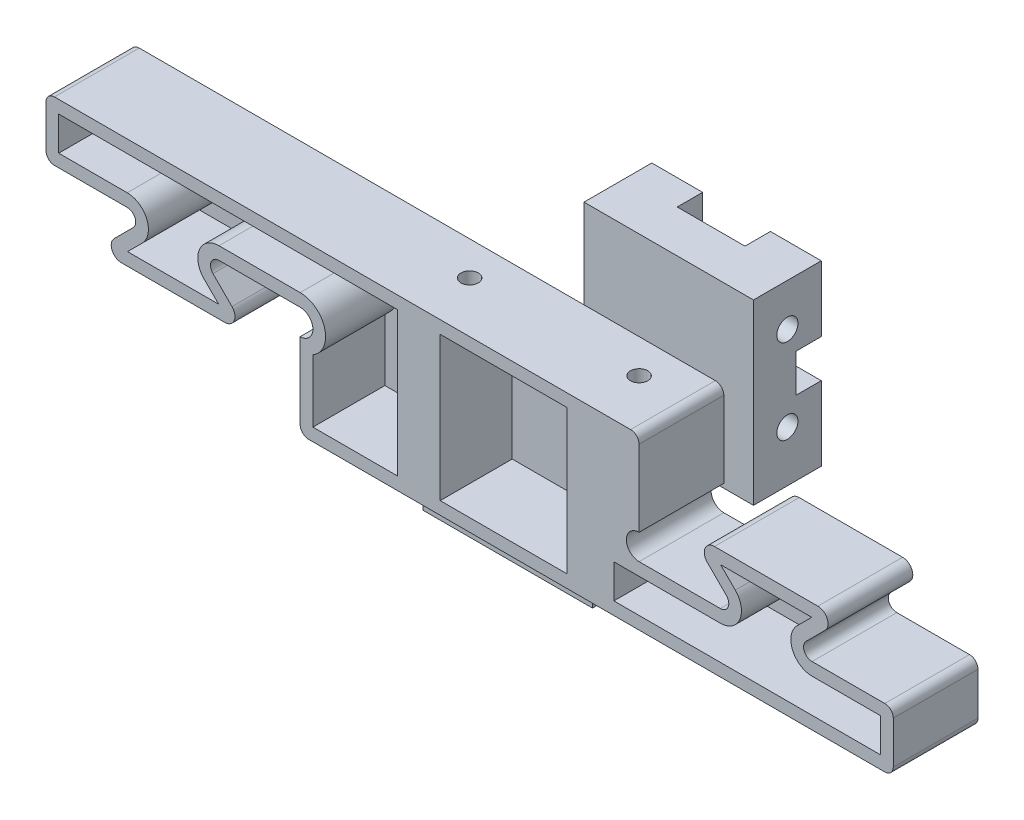
SolidWorks part; units mm, degrees
material "ABS"
ref_plane "Front Plane" through (0, 0, 0) normal (0, 0, 1) x (1, 0, 0)
ref_plane "Top Plane" through (0, 0, 0) normal (0, 1, 0) x (1, 0, 0)
ref_plane "Right Plane" through (0, 0, 0) normal (1, 0, 0) x (0, 0, -1)
sketch "Sketch1" plane through (0, 0, 0) normal (0, 0, 1) x (1, 0, 0)
  line L0 (-42.9118, -0.5) -> (16.2918, -0.5) construction
  line L2 (1, -1) -> (-19, -1)
  line L3 (1, -1) -> (1, -21)
  line L4 (1, -21) -> (-19, -21)
  line L5 (-19, -1) -> (-19, -21)
  line L6 (0, 0) -> (20, 0)
  line L7 (0, 0) -> (0, 20)
  line L8 (0, 20) -> (20, 20)
  line L9 (20, 0) -> (20, 20)
  dimension "D1" = 20
  dimension "D2" = 1
  dimension "D3" = 1
extrude "Boss-Extrude1" add sketch "Sketch1" along normal blind 8
hole_wizard "Tap Drill for M3 Tap1" positions "Sketch4" profile "Sketch3" hole size "M3" standard "DIN" end condition through all
sketch "Sketch4" plane through (20, 6.9301, -5.4582) normal (1, 0, 0) x (0, 0, -1)
  line L0 (-9.4582, 13.0699) -> (-9.4582, -24.1023) construction
  line L1 (-13.4582, 13.0699) -> (-5.4582, 13.0699) construction
  line L3 (-13.4582, 3.0699) -> (-15.7818, 3.0699) construction
  line L4 (-13.4582, -6.9301) -> (-13.4582, 13.0699) construction
  line L6 (-13.4582, -17.9301) -> (-14.075, -17.9301) construction
  line L7 (-13.4582, -27.9301) -> (-13.4582, -7.9301) construction
  point P0 (-9.4582, -12.9301)
  point P9 (-9.4582, 8.0699)
  point P11 (-9.4582, -1.9301)
  point P13 (-9.4582, -22.9301)
  dimension "D1" = 10
  dimension "D2" = 10
sketch "Sketch3" plane through (20, -6, 4) normal (0, 1, 0) x (0, 0, -1)
  line L0 (0, 0) -> (0, 39)
  line L1 (0, 39) -> (1.25, 39)
  line L2 (1.25, 39) -> (1.25, 0)
  line L5 (1.25, 0) -> (0, 0)
  line L11 (0, -6.35) -> (0, 107.95) construction
  dimension "Thru Hole Dia." = 2.5
  dimension "Thru Hole Depth" = 39
sketch "Sketch5" plane through (0, 0, 8) normal (0, 0, 1) x (1, 0, 0)
  line L0 (-19, -0.5) -> (20, -0.5) construction
  line L1 (1, -1) -> (-19, -1) construction
  line L2 (0, 0) -> (20, 0) construction
  line L3 (-19, -1) -> (-19, -21) construction
  line L4 (20, 0) -> (20, 20) construction
  line L6 (-13.5, -10.5) -> (14.5, -10.5)
  line L7 (-13.5, -10.5) -> (-13.5, 9.5)
  line L8 (-13.5, 9.5) -> (14.5, 9.5)
  line L9 (14.5, -10.5) -> (14.5, 9.5)
  line L10 (-13.5, -10.5) -> (14.5, 9.5) construction
  line L11 (-13.5, 9.5) -> (14.5, -10.5) construction
  point P10 (0.5, -0.5)
  dimension "D1" = 28
extrude "Boss-Extrude2" add sketch "Sketch5" along normal blind 8
hole_wizard "Tap Drill for M2.5 Tap1" positions "Sketch7" profile "Sketch6" hole size "M2.5" standard "DIN" end condition through all
sketch "Sketch7" plane through (0, -10.5, 0) normal (0, -1, 0) x (1, 0, 0)
  line L0 (-13.5, 12) -> (14.5, 12) construction
  line L1 (-13.5, 16) -> (-13.5, 8) construction
  line L2 (14.5, 16) -> (14.5, 8) construction
  line L4 (0.5, 16) -> (0.5, 18.815) construction
  line L5 (-13.5, 16) -> (14.5, 16) construction
  point P0 (-9.5, 12)
  point P1 (10.5, 12)
  dimension "D1" = 20
sketch "Sketch6" plane through (-9.5, -10.5, 12) normal (1, 0, 0) x (0, 0, -1)
  line L0 (0, 0) -> (0, 30.5)
  line L1 (0, 30.5) -> (1.025, 30.5)
  line L2 (1.025, 30.5) -> (1.025, 0)
  line L5 (1.025, 0) -> (0, 0)
  line L11 (0, -6.35) -> (0, 107.95) construction
  dimension "Thru Hole Dia." = 2.05
  dimension "Thru Hole Depth" = 30.5
sketch "Sketch16" plane through (0, 9.5, 0) normal (0, 1, 0) x (1, 0, 0)
  line L1 (-13.5, -16) -> (14.5, -16)
  line L2 (-13.5, -16) -> (-13.5, -18)
  line L3 (-13.5, -18) -> (14.5, -18)
  line L4 (14.5, -16) -> (14.5, -18)
  dimension "D1" = 2
extrude "Boss-Extrude3" add sketch "Sketch16" against normal up to surface (20 mm away) up to face at (-9.5, -10.5, 10.975)
ref_plane "Plane1" through (0, 0, 6.5) normal (0, 0, -1) x (-1, 0, 0)
sketch "Sketch11" plane through (0, 0, 6.5) normal (0, 0, -1) x (-1, 0, 0)
  line L0 (-20, 20) -> (0, 0) construction
  line L1 (-6, 2) -> (-14, 2)
  line L2 (-6, 2) -> (-6, 18)
  line L3 (-6, 18) -> (-14, 18)
  line L4 (-14, 2) -> (-14, 18)
  line L5 (-6, 2) -> (-14, 18) construction
  line L6 (-6, 18) -> (-14, 2) construction
  line L7 (-20, 20) -> (0, 20) construction
  line L8 (-20, 0) -> (-20, 20) construction
  line L9 (-1, -1) -> (19, -21) construction
  line L11 (13, -19) -> (5, -19)
  line L12 (13, -19) -> (13, -3)
  line L13 (13, -3) -> (5, -3)
  line L14 (5, -19) -> (5, -3)
  line L15 (13, -19) -> (5, -3) construction
  line L16 (13, -3) -> (5, -19) construction
  point P0 (-10, 10)
  point P17 (9, -11)
  dimension "D1" = 2
  dimension "D2" = 6
extrude "Cut-Extrude3" cut sketch "Sketch11" along normal blind 11
fillet "Fillet1" radius 2 8 edges at (14, 18, 3.25) (6, 18, 3.25) (6, 2, 3.25) (14, 2, 3.25) (-5, -19, 3.25) (-13, -19, 3.25) (-13, -3, 3.25) (-5, -3, 3.25)
sketch "Sketch18" plane through (0, 0, 18) normal (0, 0, 1) x (1, 0, 0)
  line L0 (-13.5, -10.5) -> (-13.5, 9.5) construction
  line L1 (14.5, 9.5) -> (16.5, 9.5)
  line L2 (14.5, 9.5) -> (14.5, -10.5)
  line L3 (14.5, -10.5) -> (16.5, -10.5)
  line L4 (16.5, 9.5) -> (16.5, -10.5)
  line L5 (-13.5, 9.5) -> (-15.5, 9.5)
  line L6 (-13.5, 9.5) -> (-13.5, -10.5)
  line L7 (-13.5, -10.5) -> (-15.5, -10.5)
  line L8 (-15.5, 9.5) -> (-15.5, -10.5)
  line L9 (-13.5, -1) -> (-13.5, -10.5) construction
  dimension "D1" = 2
  dimension "D2" = 2
extrude "Boss-Extrude4" add sketch "Sketch18" against normal up to surface (10 mm away) up to face at (0.5, -0.5, 8)
sketch "Sketch21" plane through (-15.5, 0, 0) normal (-1, 0, 0) x (0, 0, 1)
  line L1 (8, 9.5) -> (18, 9.5)
  line L2 (8, 9.5) -> (8, -10.5)
  line L3 (8, -10.5) -> (18, -10.5)
  line L4 (18, 9.5) -> (18, -10.5)
extrude "Boss-Extrude7" add sketch "Sketch21" along normal blind 8
sketch "Sketch17" plane through (0, 0, 18) normal (0, 0, 1) x (1, 0, 0)
  line L0 (16.5, -10.5) -> (46.5, -10.5)
  line L1 (46.5, -10.5) -> (46.5, -3.5)
  line L2 (16.5, -3.5) -> (16.5, -10.5)
  line L3 (16.5, -3.5) -> (28.5, -3.5)
  line L4 (28.5, -3.5) -> (22.5, 2.5)
  line L5 (22.5, 2.5) -> (40.5, 2.5)
  line L6 (34.5, -3.5) -> (40.5, 2.5)
  line L7 (34.5, -3.5) -> (46.5, -3.5)
  line L8 (16.5, -10.5) -> (16.5, 9.5) construction
  line L9 (16.5, 9.5) -> (62.7513, 9.5) construction
  line L10 (-23.5, 2.5) -> (-35.5, 2.5)
  line L11 (-29.5, -3.5) -> (-47.5, -3.5)
  line L12 (-41.5, 2.5) -> (-53.5, 2.5)
  line L13 (-53.5, 9.5) -> (-53.5, 2.5)
  line L14 (-35.5, 2.5) -> (-29.5, -3.5)
  line L15 (-23.5, 2.5) -> (-23.5, 9.5)
  line L16 (-23.5, 9.5) -> (-23.5, -10.5) construction
  line L17 (-41.5, 2.5) -> (-47.5, -3.5)
  line L18 (-23.5, 9.5) -> (-53.5, 9.5)
  line L19 (-23.5, -10.5) -> (-23.5, 9.5) construction
  line L20 (-23.5, 9.5) -> (16.5, 9.5) construction
  line L21 (-23.5, -10.5) -> (-23.5, 9.5) construction
  dimension "D1" = 45
  dimension "D2" = 7
  dimension "D3" = 6
  dimension "D4" = 24
  dimension "D5" = 12
  dimension "D6" = 18
  dimension "D7" = 45
  dimension "D8" = 30
  dimension "D9" = 45
  dimension "D10" = 45
extrude "Boss-Extrude5" add sketch "Sketch17" against normal blind 10
fillet "Fillet2" radius 1 6 edges at (34.5, -3.5, 13) (28.5, -3.5, 13) (22.5, 2.5, 13) (40.5, 2.5, 13) (46.5, -3.5, 13) (46.5, -10.5, 13)
sketch "Sketch19" plane through (0, 0, 18) normal (0, 0, 1) x (1, 0, 0)
  line L10 (13.525, -5) -> (13.525, -9)
  line L12 (11.525, -10.5) -> (11.525, 9.5) construction
  line L20 (36.8787, 1) -> (26.1213, 1)
  line L21 (26.1213, 1) -> (27.8536, -0.7322)
  line L22 (26.0858, -5) -> (15, -5)
  line L23 (15, -5) -> (15, 8)
  line L24 (15, 8) -> (-52, 8)
  line L25 (-22, 4) -> (-22, -9)
  line L26 (-22, -9) -> (45, -9)
  line L27 (45, -9) -> (45, -5)
  line L28 (45, -5) -> (36.9142, -5)
  line L29 (35.1464, -0.7322) -> (36.8787, 1)
  line L30 (36.8787, 1) -> (26.1213, 1)
  line L31 (26.1213, 1) -> (27.8536, -0.7322)
  line L32 (26.0858, -5) -> (13.525, -5)
  line L36 (13.525, -9) -> (45, -9)
  line L37 (45, -9) -> (45, -5)
  line L38 (45, -5) -> (36.9142, -5)
  line L39 (35.1464, -0.7322) -> (36.8787, 1)
  line L48 (-52, 8) -> (-52, 4)
  line L50 (-52, 4) -> (-22, 4)
  arc A8 (26.0858, -5) -> (27.8536, -0.7322) centre (26.0858, -2.5) ccw
  arc A9 (35.1464, -0.7322) -> (36.9142, -5) centre (36.9142, -2.5) ccw
  arc A10 (26.0858, -5) -> (27.8536, -0.7322) centre (26.0858, -2.5) ccw
  arc A11 (35.1464, -0.7322) -> (36.9142, -5) centre (36.9142, -2.5) ccw
  dimension "D2" = 2
  dimension "D1" = 1.5
extrude "Cut-Extrude4" cut sketch "Sketch19" against normal blind 8.5
sketch "Sketch23" plane through (0, 0, 18) normal (0, 0, 1) x (1, 0, 0)
  line L0 (13.525, -9) -> (45, -9) construction
  line L1 (-6.975, 8) -> (7.975, 8)
  line L2 (-6.975, 8) -> (-6.975, -9)
  line L3 (-6.975, -9) -> (7.975, -9)
  line L4 (7.975, 8) -> (7.975, -9)
  line L5 (-53.5, 9.5) -> (16.5, 9.5) construction
  line L6 (-8.475, -10.5) -> (-8.475, 9.5) construction
  line L7 (9.475, 9.5) -> (9.475, -10.5) construction
  dimension "D1" = 1.5
  dimension "D2" = 1.5
  dimension "D3" = 1.5
extrude "Cut-Extrude5" cut sketch "Sketch23" against normal blind 8.5
sketch "Sketch24" plane through (0, 0, 18) normal (0, 0, 1) x (1, 0, 0)
  line L0 (16.5, -3.5) -> (16.5, 9.5) construction
  line L1 (-35.5, 2.5) -> (-23.5, 2.5) construction
  line L2 (-23.5, -10.5) -> (-23.5, 2.5) construction
  circle A0 centre (16.5, -2) radius 1.5
  circle A1 centre (-23.5, 1) radius 1.5
  dimension "D1" = 3
extrude "Cut-Extrude6" cut sketch "Sketch24" against normal up to surface (10 mm away) up to face at (4.2648, -1.4464, 8)
fillet "Fillet3" radius 1 8 edges at (-53.5, 9.5, 13) (-53.5, 2.5, 13) (-41.5, 2.5, 13) (-47.5, -3.5, 13) (-35.5, 2.5, 13) (-29.5, -3.5, 13) (16.5, 9.5, 13) (-23.5, -10.5, 13)
sketch "Sketch26" plane through (0, 0, 18) normal (0, 0, 1) x (1, 0, 0)
  line L32 (-33.0858, 2.5) -> (-10.525, 2.5) construction
  line L33 (-10.525, 2.5) -> (-10.525, 9.5) construction
  line L35 (-33.0858, 4) -> (-12.025, 4)
  line L36 (-12.025, 4) -> (-12.025, 8)
  line L37 (-12.025, 8) -> (-52, 8)
  line L38 (-52, 8) -> (-52, 4)
  line L39 (-52, 4) -> (-43.9142, 4)
  line L40 (-42.1464, -0.2678) -> (-43.8787, -2)
  line L41 (-43.8787, -2) -> (-33.1213, -2)
  line L42 (-33.1213, -2) -> (-34.8536, -0.2678)
  line L43 (-10.525, 9.5) -> (-10.525, -10.5) construction
  line L48 (16.5, -0.5) -> (16.5, 8.5)
  line L49 (15.5, 9.5) -> (-52.5, 9.5)
  line L50 (-53.5, 8.5) -> (-53.5, 3.5)
  line L51 (-52.5, 2.5) -> (-43.9142, 2.5)
  line L52 (-43.2071, 0.7929) -> (-45.7929, -1.7929)
  line L53 (-45.0858, -3.5) -> (-31.9142, -3.5)
  line L54 (-31.2071, -1.7929) -> (-33.7929, 0.7929)
  line L55 (-33.0858, 2.5) -> (-23.5, 2.5)
  line L56 (-23.5, -0.5) -> (-23.5, -9.5)
  line L57 (-22.5, -10.5) -> (45.5, -10.5)
  line L58 (46.5, -9.5) -> (46.5, -4.5)
  line L59 (45.5, -3.5) -> (36.9142, -3.5)
  line L60 (36.2071, -1.7929) -> (38.7929, 0.7929)
  line L61 (38.0858, 2.5) -> (24.9142, 2.5)
  line L62 (24.2071, 0.7929) -> (26.7929, -1.7929)
  line L63 (26.0858, -3.5) -> (16.5, -3.5)
  line L65 (-10.525, 9.5) -> (-52.5, 9.5) construction
  line L66 (-53.5, 8.5) -> (-53.5, 3.5) construction
  line L67 (-52.5, 2.5) -> (-43.9142, 2.5) construction
  line L68 (-43.2071, 0.7929) -> (-45.7929, -1.7929) construction
  line L69 (-45.0858, -3.5) -> (-31.9142, -3.5) construction
  line L70 (-31.2071, -1.7929) -> (-33.7929, 0.7929) construction
  arc A30 (-52, 8) -> (-52, 8) centre (-52, 8) ccw
  arc A31 (-52, 4) -> (-52, 4) centre (-52, 4) ccw
  arc A32 (-42.1464, -0.2678) -> (-43.9142, 4) centre (-43.9142, 1.5) ccw
  arc A33 (-43.8787, -2) -> (-43.8787, -2) centre (-43.8787, -2) ccw
  arc A34 (-33.1213, -2) -> (-33.1213, -2) centre (-33.1213, -2) ccw
  arc A35 (-33.0858, 4) -> (-34.8536, -0.2678) centre (-33.0858, 1.5) ccw
  arc A45 (16.5, 8.5) -> (15.5, 9.5) centre (15.5, 8.5) ccw
  arc A46 (-52.5, 9.5) -> (-53.5, 8.5) centre (-52.5, 8.5) ccw
  arc A47 (-53.5, 3.5) -> (-52.5, 2.5) centre (-52.5, 3.5) ccw
  arc A48 (-43.2071, 0.7929) -> (-43.9142, 2.5) centre (-43.9142, 1.5) ccw
  arc A49 (-45.7929, -1.7929) -> (-45.0858, -3.5) centre (-45.0858, -2.5) ccw
  arc A50 (-31.9142, -3.5) -> (-31.2071, -1.7929) centre (-31.9142, -2.5) ccw
  arc A51 (-33.0858, 2.5) -> (-33.7929, 0.7929) centre (-33.0858, 1.5) ccw
  arc A52 (-23.5, -0.5) -> (-23.5, 2.5) centre (-23.5, 1) ccw
  arc A53 (45.5, -10.5) -> (46.5, -9.5) centre (45.5, -9.5) ccw
  arc A54 (46.5, -4.5) -> (45.5, -3.5) centre (45.5, -4.5) ccw
  arc A55 (36.2071, -1.7929) -> (36.9142, -3.5) centre (36.9142, -2.5) ccw
  arc A56 (38.7929, 0.7929) -> (38.0858, 2.5) centre (38.0858, 1.5) ccw
  arc A57 (24.9142, 2.5) -> (24.2071, 0.7929) centre (24.9142, 1.5) ccw
  arc A58 (26.0858, -3.5) -> (26.7929, -1.7929) centre (26.0858, -2.5) ccw
  arc A59 (16.5, -0.5) -> (16.5, -3.5) centre (16.5, -2) ccw
  arc A61 (-52.5, 9.5) -> (-53.5, 8.5) centre (-52.5, 8.5) ccw construction
  arc A62 (-53.5, 3.5) -> (-52.5, 2.5) centre (-52.5, 3.5) ccw construction
  arc A63 (-43.2071, 0.7929) -> (-43.9142, 2.5) centre (-43.9142, 1.5) ccw construction
  arc A64 (-45.7929, -1.7929) -> (-45.0858, -3.5) centre (-45.0858, -2.5) ccw construction
  arc A65 (-31.9142, -3.5) -> (-31.2071, -1.7929) centre (-31.9142, -2.5) ccw construction
  arc A66 (-33.0858, 2.5) -> (-33.7929, 0.7929) centre (-33.0858, 1.5) ccw construction
  arc A73 (-23.5, -9.5) -> (-22.5, -10.5) centre (-22.5, -9.5) ccw
  dimension "D1" = 0
  dimension "D3" = 1.5
extrude "Cut-Extrude7" cut sketch "Sketch26" against normal blind 8.5
sketch "Sketch27" plane through (0, 0, 18) normal (0, 0, 1) x (1, 0, 0)
  line L1 (-12.025, 8) -> (-52, 8) construction
  line L2 (-23.5, 4) -> (-23.5, 8)
  line L3 (-22, -1.5981) -> (-22, -9)
  line L5 (-12.025, 8) -> (-12.025, -9)
  line L6 (-12.025, -9) -> (-22, -9)
  line L7 (-6.975, -9) -> (7.975, -9) construction
  line L8 (-23.5, -0.5) -> (-23.5, -9.5) construction
  line L9 (-22, -1.5981) -> (-22, -9.5) construction
  line L10 (-33.0858, 4) -> (-12.025, 4) construction
  line L11 (-23.5, 8) -> (-12.025, 8)
  line L16 (16.5, -0.5) -> (16.5, 8.5)
  line L17 (15.5, 9.5) -> (-52.5, 9.5)
  line L18 (-53.5, 8.5) -> (-53.5, 3.5)
  line L19 (-52.5, 2.5) -> (-43.9142, 2.5)
  line L20 (-43.2071, 0.7929) -> (-45.7929, -1.7929)
  line L21 (-45.0858, -3.5) -> (-31.9142, -3.5)
  line L22 (-31.2071, -1.7929) -> (-33.7929, 0.7929)
  line L23 (-33.0858, 2.5) -> (-23.5, 2.5)
  line L24 (-23.5, -0.5) -> (-23.5, -9.5)
  line L25 (-22.5, -10.5) -> (45.5, -10.5)
  line L26 (46.5, -9.5) -> (46.5, -4.5)
  line L27 (45.5, -3.5) -> (36.9142, -3.5)
  line L28 (36.2071, -1.7929) -> (38.7929, 0.7929)
  line L29 (38.0858, 2.5) -> (24.9142, 2.5)
  line L30 (24.2071, 0.7929) -> (26.7929, -1.7929)
  line L31 (26.0858, -3.5) -> (16.5, -3.5)
  line L45 (-22, 3.5981) -> (-22, 8) construction
  line L46 (-23.5, 2.5) -> (-23.5, 8) construction
  arc A0 (-22, -1.5981) -> (-23.5, 4) centre (-23.5, 1) ccw
  arc A1 (-22, -1.5981) -> (-22, 3.5981) centre (-23.5, 1) ccw construction
  arc A15 (16.5, 8.5) -> (15.5, 9.5) centre (15.5, 8.5) ccw
  arc A16 (-52.5, 9.5) -> (-53.5, 8.5) centre (-52.5, 8.5) ccw
  arc A17 (-53.5, 3.5) -> (-52.5, 2.5) centre (-52.5, 3.5) ccw
  arc A18 (-43.2071, 0.7929) -> (-43.9142, 2.5) centre (-43.9142, 1.5) ccw
  arc A19 (-45.7929, -1.7929) -> (-45.0858, -3.5) centre (-45.0858, -2.5) ccw
  arc A20 (-31.9142, -3.5) -> (-31.2071, -1.7929) centre (-31.9142, -2.5) ccw
  arc A21 (-33.0858, 2.5) -> (-33.7929, 0.7929) centre (-33.0858, 1.5) ccw
  arc A22 (-23.5, -0.5) -> (-23.5, 2.5) centre (-23.5, 1) ccw
  arc A23 (45.5, -10.5) -> (46.5, -9.5) centre (45.5, -9.5) ccw
  arc A24 (46.5, -4.5) -> (45.5, -3.5) centre (45.5, -4.5) ccw
  arc A25 (36.2071, -1.7929) -> (36.9142, -3.5) centre (36.9142, -2.5) ccw
  arc A26 (38.7929, 0.7929) -> (38.0858, 2.5) centre (38.0858, 1.5) ccw
  arc A27 (24.9142, 2.5) -> (24.2071, 0.7929) centre (24.9142, 1.5) ccw
  arc A28 (26.0858, -3.5) -> (26.7929, -1.7929) centre (26.0858, -2.5) ccw
  arc A29 (16.5, -0.5) -> (16.5, -3.5) centre (16.5, -2) ccw
  arc A32 (-23.5, -9.5) -> (-22.5, -10.5) centre (-22.5, -9.5) ccw
  arc A37 (-23.5, -0.5) -> (-23.5, 2.5) centre (-23.5, 1) ccw construction
  dimension "D1" = 0
  dimension "D2" = 1.5
extrude "Cut-Extrude8" cut sketch "Sketch27" against normal blind 8.5
sketch "Sketch28" plane through (0, 0, 0) normal (0, 0, -1) x (-1, 0, 0)
  line L0 (-20, 20) -> (0, 0) construction
  line L1 (-20, 0) -> (-20, 20) construction
  line L2 (-1.5, 7.75) -> (-18.5, 7.75)
  line L3 (-1.5, 7.75) -> (-1.5, 12.25)
  line L4 (-1.5, 12.25) -> (-18.5, 12.25)
  line L5 (-18.5, 7.75) -> (-18.5, 12.25)
  line L6 (-1.5, 7.75) -> (-18.5, 12.25) construction
  line L7 (-1.5, 12.25) -> (-18.5, 7.75) construction
  line L8 (-1, -1) -> (19, -21) construction
  line L9 (-1, -21) -> (-1, -1) construction
  line L10 (17.5, -13.25) -> (0.5, -13.25)
  line L11 (17.5, -13.25) -> (17.5, -8.75)
  line L12 (17.5, -8.75) -> (0.5, -8.75)
  line L13 (0.5, -13.25) -> (0.5, -8.75)
  line L14 (17.5, -13.25) -> (0.5, -8.75) construction
  line L15 (17.5, -8.75) -> (0.5, -13.25) construction
  line L16 (-14, 6.25) -> (-20, 6.25) construction
  point P4 (-10, 10)
  point P15 (9, -11)
  dimension "D1" = 1.5
  dimension "D2" = 1.5
  dimension "D3" = 1.5
extrude "Cut-Extrude9" cut sketch "Sketch28" against normal blind 6.5
sketch "Sketch30" plane through (0, 0, 0) normal (0, 0, -1) x (-1, 0, 0)
  line L0 (-1, -21) -> (-1, -1) construction
  line L1 (-1, -13.25) -> (19, -13.25)
  line L2 (-1, -13.25) -> (-1, -8.75)
  line L3 (-1, -8.75) -> (19, -8.75)
  line L4 (19, -13.25) -> (19, -8.75)
  line L5 (19, -1) -> (19, -21) construction
  line L6 (17.5, -8.75) -> (13, -8.75) construction
  line L7 (0.5, -13.25) -> (5, -13.25) construction
  line L8 (-20, 0) -> (-20, 20) construction
  line L9 (-20, 7.75) -> (0, 7.75)
  line L10 (-20, 7.75) -> (-20, 12.25)
  line L11 (-20, 12.25) -> (0, 12.25)
  line L12 (0, 7.75) -> (0, 12.25)
  line L13 (0, 20) -> (0, 0) construction
  line L14 (-1.5, 12.25) -> (-6, 12.25) construction
  line L15 (-18.5, 7.75) -> (-14, 7.75) construction
extrude "Cut-Extrude10" cut sketch "Sketch30" against normal blind 3
sketch "Sketch31" plane through (0, 0, 0) normal (0, 0, -1) x (-1, 0, 0)
  line L0 (-20, 20) -> (0, 20) construction
  line L1 (-14, 20) -> (-6, 20)
  line L2 (-14, 20) -> (-14, 0)
  line L3 (-14, 0) -> (-6, 0)
  line L4 (-6, 20) -> (-6, 0)
  line L6 (-14, 20) -> (-6, 0) construction
  line L7 (-14, 12.25) -> (-14, 16) construction
  line L10 (-6, 4) -> (-6, 7.75) construction
  line L11 (0, 0) -> (-20, 0) construction
  line L12 (-1, -1) -> (19, -1) construction
  line L13 (5, -1) -> (13, -1)
  line L14 (5, -1) -> (5, -21)
  line L15 (5, -21) -> (13, -21)
  line L16 (13, -1) -> (13, -21)
  line L17 (19, -21) -> (-1, -21) construction
  line L18 (13, -13.25) -> (13, -17) construction
  line L19 (5, -13.25) -> (5, -17) construction
extrude "Cut-Extrude11" cut sketch "Sketch31" against normal blind 3
sketch "Sketch32" plane through (0, 0, 8) normal (0, 0, -1) x (-1, 0, 0)
  line L0 (-25.3971, 2.5) -> (-37.6029, 2.5)
  line L1 (-38.0858, 2.5) -> (-24.9142, 2.5) construction
  line L2 (-38.4515, 0.4515) -> (-37.0989, -0.9011)
  line L3 (-36.2071, -1.7929) -> (-38.7929, 0.7929) construction
  line L4 (-24.5485, 0.4515) -> (-25.5, -0.5)
  line L5 (-24.2071, 0.7929) -> (-26.7929, -1.7929) construction
  line L6 (-37.0989, -0.9011) -> (-41.0529, -0.9011)
  line L7 (-41.0529, -0.9011) -> (-41.0529, 4.6991)
  line L8 (-41.0529, 4.6991) -> (-23.0717, 4.6991)
  line L9 (-23.0717, 4.6991) -> (-23.0717, -0.5)
  line L10 (-23.0717, -0.5) -> (-25.5, -0.5)
  line L11 (32.5, -0.5) -> (31.5485, -1.4515)
  line L12 (31.2071, -1.7929) -> (33.7929, 0.7929) construction
  line L13 (32.3971, -3.5) -> (44.6029, -3.5)
  line L14 (45.4515, -1.4515) -> (44.5, -0.5)
  line L15 (43.2071, 0.7929) -> (45.7929, -1.7929) construction
  line L16 (44.5, -0.5) -> (48.3434, -0.5)
  line L17 (48.3434, -0.5) -> (48.3434, -6.9265)
  line L18 (48.3434, -6.9265) -> (26.8268, -6.9265)
  line L19 (26.8268, -6.9265) -> (26.8268, -0.5)
  line L20 (26.8268, -0.5) -> (32.5, -0.5)
  line L21 (45.0858, -3.5) -> (31.9142, -3.5) construction
  arc A0 (-37.6029, 2.5) -> (-38.4515, 0.4515) centre (-37.6029, 1.3) ccw
  arc A1 (-25.3971, 2.5) -> (-24.5485, 0.4515) centre (-25.3971, 1.3) cw
  arc A2 (31.5485, -1.4515) -> (32.3971, -3.5) centre (32.3971, -2.3) ccw
  arc A3 (45.4515, -1.4515) -> (44.6029, -3.5) centre (44.6029, -2.3) cw
  point P14 (-22.5, 2.5)
  dimension "D1" = 1.2
  dimension "D2" = 1.2
  dimension "D3" = 1.2
  dimension "D4" = 1.2
extrude "Cut-Extrude12" cut sketch "Sketch32" against normal blind 10
sketch "Sketch34" plane through (0, 0, 8) normal (0, 0, -1) x (-1, 0, 0)
  line L0 (-20, 0) -> (19, 0)
  line L1 (19, -1) -> (-20, -1)
  line L2 (-20, 0) -> (-20, -1)
  line L3 (19, -1) -> (19, 0)
extrude "Boss-Extrude8" add sketch "Sketch34" along normal up to surface (8 mm away)
sketch "Sketch35" plane through (0, 0, 6.5) normal (0, 0, -1) x (-1, 0, 0)
  line L0 (-6, 4) -> (-6, 7.75) construction
  line L1 (-6, 7.75) -> (-1.5, 7.75) construction
  line L2 (-1.5, 7.75) -> (-1.5, 12.25) construction
  line L3 (-1.5, 12.25) -> (-6, 12.25) construction
  line L4 (-6, 12.25) -> (-6, 16) construction
  line L5 (-8, 18) -> (-12, 18) construction
  line L6 (-14, 16) -> (-14, 12.25) construction
  line L7 (-14, 12.25) -> (-18.5, 12.25) construction
  line L8 (-18.5, 12.25) -> (-18.5, 7.75) construction
  line L9 (-18.5, 7.75) -> (-14, 7.75) construction
  line L10 (-14, 7.75) -> (-14, 4) construction
  line L11 (-12, 2) -> (-8, 2) construction
  line L12 (13, -17) -> (13, -13.25) construction
  line L13 (13, -13.25) -> (17.5, -13.25) construction
  line L14 (17.5, -13.25) -> (17.5, -8.75) construction
  line L15 (17.5, -8.75) -> (13, -8.75) construction
  line L16 (13, -8.75) -> (13, -5) construction
  line L17 (11, -3) -> (7, -3) construction
  line L18 (5, -5) -> (5, -8.75) construction
  line L19 (5, -8.75) -> (0.5, -8.75) construction
  line L20 (0.5, -8.75) -> (0.5, -13.25) construction
  line L21 (0.5, -13.25) -> (5, -13.25) construction
  line L22 (5, -13.25) -> (5, -17) construction
  line L23 (7, -19) -> (11, -19) construction
  line L24 (-6, 4) -> (-6, 7.75)
  line L25 (-6, 7.75) -> (-1.5, 7.75)
  line L26 (-1.5, 7.75) -> (-1.5, 12.25)
  line L27 (-1.5, 12.25) -> (-6, 12.25)
  line L28 (-6, 12.25) -> (-6, 16)
  line L29 (-8, 18) -> (-12, 18)
  line L30 (-14, 16) -> (-14, 12.25)
  line L31 (-14, 12.25) -> (-18.5, 12.25)
  line L32 (-18.5, 12.25) -> (-18.5, 7.75)
  line L33 (-18.5, 7.75) -> (-14, 7.75)
  line L34 (-14, 7.75) -> (-14, 4)
  line L35 (-12, 2) -> (-8, 2)
  line L36 (13, -17) -> (13, -13.25)
  line L37 (13, -13.25) -> (17.5, -13.25)
  line L38 (17.5, -13.25) -> (17.5, -8.75)
  line L39 (17.5, -8.75) -> (13, -8.75)
  line L40 (13, -8.75) -> (13, -5)
  line L41 (11, -3) -> (7, -3)
  line L42 (5, -5) -> (5, -8.75)
  line L43 (5, -8.75) -> (0.5, -8.75)
  line L44 (0.5, -8.75) -> (0.5, -13.25)
  line L45 (0.5, -13.25) -> (5, -13.25)
  line L46 (5, -13.25) -> (5, -17)
  line L47 (7, -19) -> (11, -19)
  arc A0 (-6, 16) -> (-8, 18) centre (-8, 16) ccw construction
  arc A1 (-12, 18) -> (-14, 16) centre (-12, 16) ccw construction
  arc A2 (-14, 4) -> (-12, 2) centre (-12, 4) ccw construction
  arc A3 (-8, 2) -> (-6, 4) centre (-8, 4) ccw construction
  arc A4 (13, -5) -> (11, -3) centre (11, -5) ccw construction
  arc A5 (7, -3) -> (5, -5) centre (7, -5) ccw construction
  arc A6 (5, -17) -> (7, -19) centre (7, -17) ccw construction
  arc A7 (11, -19) -> (13, -17) centre (11, -17) ccw construction
  arc A8 (-6, 16) -> (-8, 18) centre (-8, 16) ccw
  arc A9 (-12, 18) -> (-14, 16) centre (-12, 16) ccw
  arc A10 (-14, 4) -> (-12, 2) centre (-12, 4) ccw
  arc A11 (-8, 2) -> (-6, 4) centre (-8, 4) ccw
  arc A12 (13, -5) -> (11, -3) centre (11, -5) ccw
  arc A13 (7, -3) -> (5, -5) centre (7, -5) ccw
  arc A14 (5, -17) -> (7, -19) centre (7, -17) ccw
  arc A15 (11, -19) -> (13, -17) centre (11, -17) ccw
extrude "Boss-Extrude9" add sketch "Sketch35" along normal offset from surface (2.5 mm away) 1 separate body
